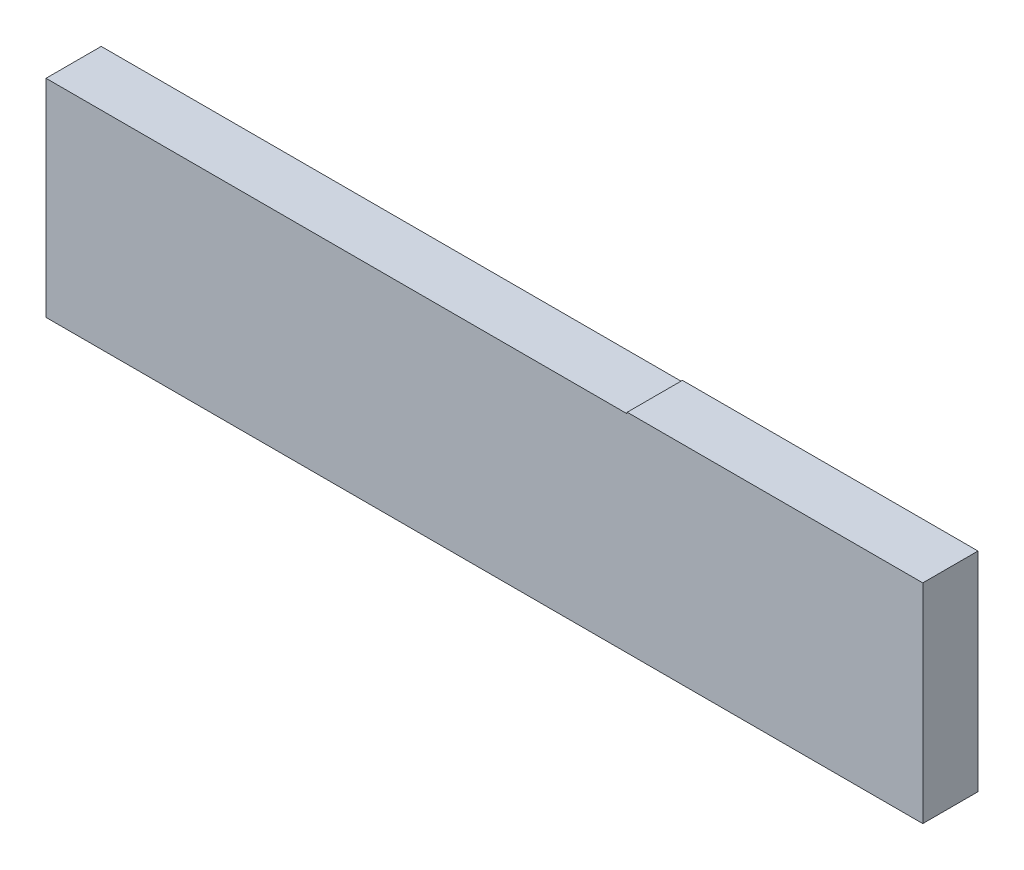
SolidWorks part; units mm, degrees
ref_plane "Ebene vorne" through (0, 0, 0) normal (0, 0, 1) x (1, 0, 0)
ref_plane "Ebene oben" through (0, 0, 0) normal (0, 1, 0) x (1, 0, 0)
ref_plane "Ebene rechts" through (0, 0, 0) normal (1, 0, 0) x (0, 0, -1)
sketch "Skizze1" plane through (0, 0, 0) normal (0, 0, 1) x (1, 0, 0)
  line L0 (42.0949, 15) -> (42.0949, 15.1)
  line L1 (0, 0) -> (42.0949, 0)
  line L2 (0, 0) -> (0, 15)
  line L3 (0, 15) -> (42.0949, 15)
  line L5 (42.0949, 15.1) -> (63.5023, 15.1)
  line L6 (63.5023, 15.1) -> (63.5023, 0)
  line L7 (63.5023, 0) -> (42.0949, 0)
  point P5 (38.0642, 15)
  point P9 (49.2554, 15.1)
  point P10 (0, 0)
  point P11 (0, 0)
  point P12 (42.0949, 15)
  dimension "D1" = 15
  dimension "D2" = 15.1
extrude "Aufsatz-Linear austragen1" add sketch "Skizze1" along normal blind 4
